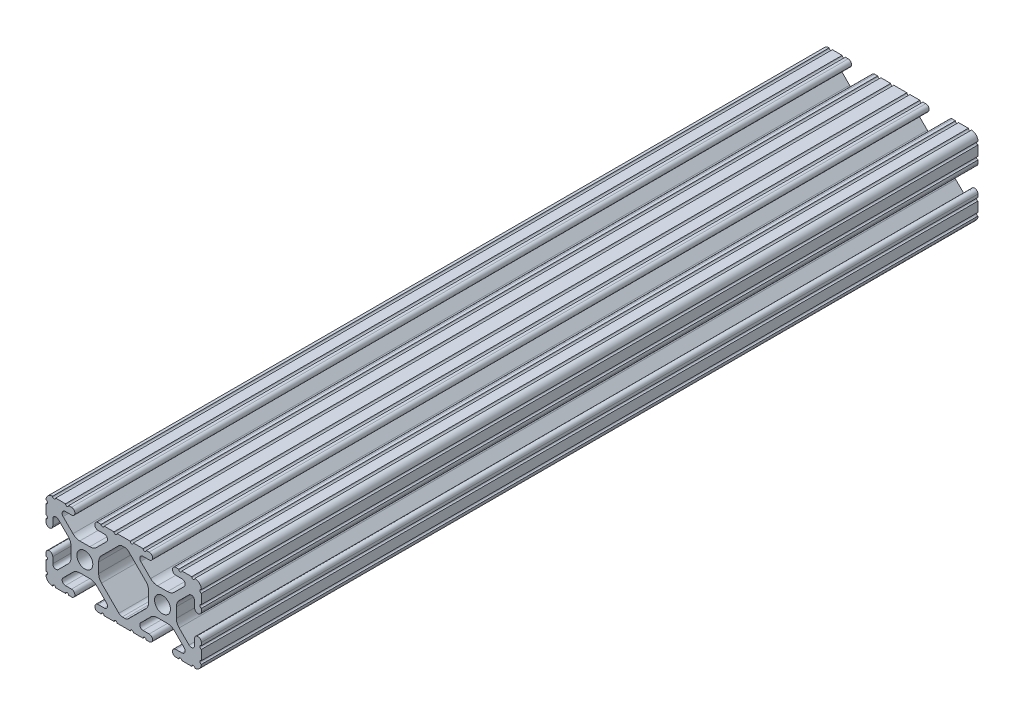
SolidWorks part; units mm, degrees
material "6105-T5 Aluminum"
ref_plane "Front Plane" through (0, 0, 0) normal (0, 0, 1) x (1, 0, 0)
ref_plane "Top Plane" through (0, 0, 0) normal (0, 1, 0) x (1, 0, 0)
ref_plane "Right Plane" through (0, 0, 0) normal (1, 0, 0) x (0, 0, -1)
sketch "Sketch1" plane through (0, 0, 0) normal (0, 0, 1) x (1, 0, 0)
  line L0 (-8.1828, -1.6394) -> (-8.1828, 1.6394)
  line L1 (-7.2529, 3.8844) -> (-1.5656, 9.5718)
  line L2 (-0.452, 10.033) -> (0.452, 10.033)
  line L3 (1.5656, 9.5718) -> (7.2529, 3.8844)
  line L4 (8.1828, 1.6394) -> (8.1828, -1.6394)
  line L5 (7.2529, -3.8844) -> (1.5656, -9.5718)
  line L6 (0.452, -10.033) -> (-0.452, -10.033)
  line L7 (-1.5656, -9.5718) -> (-7.2529, -3.8844)
  line L8 (25.4, -10.5918) -> (25.4, -10.5664)
  line L9 (25.4, -9.5504) -> (25.4, -6.3246)
  line L10 (25.4, -5.3086) -> (25.4, -4.3561)
  line L11 (23.1902, -4.3561) -> (23.1902, -6.3701)
  line L12 (21.3817, -7.1192) -> (18.1471, -3.8846)
  line L13 (17.2172, -1.6396) -> (17.2172, 1.6396)
  line L14 (18.1471, 3.8846) -> (21.3817, 7.1192)
  line L15 (23.1902, 6.3701) -> (23.1902, 4.3561)
  line L16 (25.4, 4.3561) -> (25.4, 5.3086)
  line L17 (25.4, 6.3246) -> (25.4, 9.5504)
  line L18 (25.4, 10.5664) -> (25.4, 10.5918)
  line L19 (23.2918, 12.7) -> (23.2664, 12.7)
  line L20 (22.2504, 12.7) -> (19.0246, 12.7)
  line L21 (18.0086, 12.7) -> (17.0561, 12.7)
  line L22 (17.0561, 10.4902) -> (19.0701, 10.4902)
  line L23 (19.8192, 8.6817) -> (16.5846, 5.4471)
  line L24 (14.3396, 4.5172) -> (11.0604, 4.5172)
  line L25 (8.8154, 5.4471) -> (5.5808, 8.6817)
  line L26 (6.3299, 10.4902) -> (8.3439, 10.4902)
  line L27 (8.3439, 12.7) -> (7.3914, 12.7)
  line L28 (6.3754, 12.7) -> (3.1496, 12.7)
  line L29 (2.1336, 12.7) -> (-2.1336, 12.7)
  line L30 (-3.1496, 12.7) -> (-6.3754, 12.7)
  line L31 (-7.3914, 12.7) -> (-8.3439, 12.7)
  line L32 (-8.3439, 10.4902) -> (-6.3299, 10.4902)
  line L33 (-5.5808, 8.6817) -> (-8.8154, 5.4471)
  line L34 (-11.0604, 4.5172) -> (-14.3396, 4.5172)
  line L35 (-16.5846, 5.4471) -> (-19.8192, 8.6817)
  line L36 (-19.0701, 10.4902) -> (-17.0561, 10.4902)
  line L37 (-17.0561, 12.7) -> (-18.0086, 12.7)
  line L38 (-19.0246, 12.7) -> (-22.2504, 12.7)
  line L39 (-23.2664, 12.7) -> (-23.2918, 12.7)
  line L40 (-25.4, 10.5918) -> (-25.4, 10.5664)
  line L41 (-25.4, 9.5504) -> (-25.4, 6.3246)
  line L42 (-25.4, 5.3086) -> (-25.4, 4.3561)
  line L43 (-23.1902, 4.3561) -> (-23.1902, 6.3701)
  line L44 (-21.3817, 7.1192) -> (-18.1471, 3.8846)
  line L45 (-17.2172, 1.6396) -> (-17.2172, -1.6396)
  line L46 (-18.1471, -3.8846) -> (-21.3817, -7.1192)
  line L47 (-23.1902, -6.3701) -> (-23.1902, -4.3561)
  line L48 (-25.4, -4.3561) -> (-25.4, -5.3086)
  line L49 (-25.4, -6.3246) -> (-25.4, -9.5504)
  line L50 (-25.4, -10.5664) -> (-25.4, -10.5918)
  line L51 (-23.2918, -12.7) -> (-23.2664, -12.7)
  line L52 (-22.2504, -12.7) -> (-19.0246, -12.7)
  line L53 (-18.0086, -12.7) -> (-17.0561, -12.7)
  line L54 (-17.0561, -10.4902) -> (-19.0701, -10.4902)
  line L55 (-19.8192, -8.6817) -> (-16.5846, -5.4471)
  line L56 (-14.3396, -4.5172) -> (-11.0604, -4.5172)
  line L57 (-8.8154, -5.4471) -> (-5.5808, -8.6817)
  line L58 (-6.3299, -10.4902) -> (-8.3439, -10.4902)
  line L59 (-8.3439, -12.7) -> (-7.3914, -12.7)
  line L60 (-6.3754, -12.7) -> (-3.1496, -12.7)
  line L61 (-2.1336, -12.7) -> (2.1336, -12.7)
  line L62 (3.1496, -12.7) -> (6.3754, -12.7)
  line L63 (7.3914, -12.7) -> (8.3439, -12.7)
  line L64 (8.3439, -10.4902) -> (6.3299, -10.4902)
  line L65 (5.5808, -8.6817) -> (8.8154, -5.4471)
  line L66 (11.0604, -4.5172) -> (14.3396, -4.5172)
  line L67 (16.5846, -5.4471) -> (19.8192, -8.6817)
  line L68 (19.0701, -10.4902) -> (17.0561, -10.4902)
  line L69 (17.0561, -12.7) -> (18.0086, -12.7)
  line L70 (19.0246, -12.7) -> (22.2504, -12.7)
  line L71 (23.2664, -12.7) -> (23.2918, -12.7)
  circle A0 centre (-12.7, 0) radius 2.6035
  circle A1 centre (12.7, 0) radius 2.6035
  arc A2 (-8.1828, -1.6394) -> (-7.2529, -3.8844) centre (-5.0078, -1.6394) ccw
  arc A3 (-7.2529, 3.8844) -> (-8.1828, 1.6394) centre (-5.0078, 1.6394) ccw
  arc A4 (-0.452, 10.033) -> (-1.5656, 9.5718) centre (-0.452, 8.4582) ccw
  arc A5 (1.5656, 9.5718) -> (0.452, 10.033) centre (0.452, 8.4582) ccw
  arc A6 (8.1828, 1.6394) -> (7.2529, 3.8844) centre (5.0078, 1.6394) ccw
  arc A7 (7.2529, -3.8844) -> (8.1828, -1.6394) centre (5.0078, -1.6394) ccw
  arc A8 (0.452, -10.033) -> (1.5656, -9.5718) centre (0.452, -8.4582) ccw
  arc A9 (-1.5656, -9.5718) -> (-0.452, -10.033) centre (-0.452, -8.4582) ccw
  arc A10 (23.2918, -12.7) -> (25.4, -10.5918) centre (23.2918, -10.5918) ccw
  arc A11 (25.4, -9.5504) -> (25.4, -10.5664) centre (25.4, -10.0584) ccw
  arc A12 (25.4, -5.3086) -> (25.4, -6.3246) centre (25.4, -5.8166) ccw
  arc A13 (25.4, -4.3561) -> (23.1902, -4.3561) centre (24.2951, -4.3561) ccw
  arc A14 (21.3817, -7.1192) -> (23.1902, -6.3701) centre (22.1308, -6.3701) ccw
  arc A15 (17.2172, -1.6396) -> (18.1471, -3.8846) centre (20.3922, -1.6396) ccw
  arc A16 (18.1471, 3.8846) -> (17.2172, 1.6396) centre (20.3922, 1.6396) ccw
  arc A17 (23.1902, 6.3701) -> (21.3817, 7.1192) centre (22.1308, 6.3701) ccw
  arc A18 (23.1902, 4.3561) -> (25.4, 4.3561) centre (24.2951, 4.3561) ccw
  arc A19 (25.4, 6.3246) -> (25.4, 5.3086) centre (25.4, 5.8166) ccw
  arc A20 (25.4, 10.5664) -> (25.4, 9.5504) centre (25.4, 10.0584) ccw
  arc A21 (25.4, 10.5918) -> (23.2918, 12.7) centre (23.2918, 10.5918) ccw
  arc A22 (22.2504, 12.7) -> (23.2664, 12.7) centre (22.7584, 12.7) ccw
  arc A23 (18.0086, 12.7) -> (19.0246, 12.7) centre (18.5166, 12.7) ccw
  arc A24 (17.0561, 12.7) -> (17.0561, 10.4902) centre (17.0561, 11.5951) ccw
  arc A25 (19.8192, 8.6817) -> (19.0701, 10.4902) centre (19.0701, 9.4308) ccw
  arc A26 (14.3396, 4.5172) -> (16.5846, 5.4471) centre (14.3396, 7.6922) ccw
  arc A27 (8.8154, 5.4471) -> (11.0604, 4.5172) centre (11.0604, 7.6922) ccw
  arc A28 (6.3299, 10.4902) -> (5.5808, 8.6817) centre (6.3299, 9.4308) ccw
  arc A29 (8.3439, 10.4902) -> (8.3439, 12.7) centre (8.3439, 11.5951) ccw
  arc A30 (6.3754, 12.7) -> (7.3914, 12.7) centre (6.8834, 12.7) ccw
  arc A31 (2.1336, 12.7) -> (3.1496, 12.7) centre (2.6416, 12.7) ccw
  arc A32 (-3.1496, 12.7) -> (-2.1336, 12.7) centre (-2.6416, 12.7) ccw
  arc A33 (-7.3914, 12.7) -> (-6.3754, 12.7) centre (-6.8834, 12.7) ccw
  arc A34 (-8.3439, 12.7) -> (-8.3439, 10.4902) centre (-8.3439, 11.5951) ccw
  arc A35 (-5.5808, 8.6817) -> (-6.3299, 10.4902) centre (-6.3299, 9.4308) ccw
  arc A36 (-11.0604, 4.5172) -> (-8.8154, 5.4471) centre (-11.0604, 7.6922) ccw
  arc A37 (-16.5846, 5.4471) -> (-14.3396, 4.5172) centre (-14.3396, 7.6922) ccw
  arc A38 (-19.0701, 10.4902) -> (-19.8192, 8.6817) centre (-19.0701, 9.4308) ccw
  arc A39 (-17.0561, 10.4902) -> (-17.0561, 12.7) centre (-17.0561, 11.5951) ccw
  arc A40 (-19.0246, 12.7) -> (-18.0086, 12.7) centre (-18.5166, 12.7) ccw
  arc A41 (-23.2664, 12.7) -> (-22.2504, 12.7) centre (-22.7584, 12.7) ccw
  arc A42 (-23.2918, 12.7) -> (-25.4, 10.5918) centre (-23.2918, 10.5918) ccw
  arc A43 (-25.4, 9.5504) -> (-25.4, 10.5664) centre (-25.4, 10.0584) ccw
  arc A44 (-25.4, 5.3086) -> (-25.4, 6.3246) centre (-25.4, 5.8166) ccw
  arc A45 (-25.4, 4.3561) -> (-23.1902, 4.3561) centre (-24.2951, 4.3561) ccw
  arc A46 (-21.3817, 7.1192) -> (-23.1902, 6.3701) centre (-22.1308, 6.3701) ccw
  arc A47 (-17.2172, 1.6396) -> (-18.1471, 3.8846) centre (-20.3922, 1.6396) ccw
  arc A48 (-18.1471, -3.8846) -> (-17.2172, -1.6396) centre (-20.3922, -1.6396) ccw
  arc A49 (-23.1902, -6.3701) -> (-21.3817, -7.1192) centre (-22.1308, -6.3701) ccw
  arc A50 (-23.1902, -4.3561) -> (-25.4, -4.3561) centre (-24.2951, -4.3561) ccw
  arc A51 (-25.4, -6.3246) -> (-25.4, -5.3086) centre (-25.4, -5.8166) ccw
  arc A52 (-25.4, -10.5664) -> (-25.4, -9.5504) centre (-25.4, -10.0584) ccw
  arc A53 (-25.4, -10.5918) -> (-23.2918, -12.7) centre (-23.2918, -10.5918) ccw
  arc A54 (-22.2504, -12.7) -> (-23.2664, -12.7) centre (-22.7584, -12.7) ccw
  arc A55 (-18.0086, -12.7) -> (-19.0246, -12.7) centre (-18.5166, -12.7) ccw
  arc A56 (-17.0561, -12.7) -> (-17.0561, -10.4902) centre (-17.0561, -11.5951) ccw
  arc A57 (-19.8192, -8.6817) -> (-19.0701, -10.4902) centre (-19.0701, -9.4308) ccw
  arc A58 (-14.3396, -4.5172) -> (-16.5846, -5.4471) centre (-14.3396, -7.6922) ccw
  arc A59 (-8.8154, -5.4471) -> (-11.0604, -4.5172) centre (-11.0604, -7.6922) ccw
  arc A60 (-6.3299, -10.4902) -> (-5.5808, -8.6817) centre (-6.3299, -9.4308) ccw
  arc A61 (-8.3439, -10.4902) -> (-8.3439, -12.7) centre (-8.3439, -11.5951) ccw
  arc A62 (-6.3754, -12.7) -> (-7.3914, -12.7) centre (-6.8834, -12.7) ccw
  arc A63 (-2.1336, -12.7) -> (-3.1496, -12.7) centre (-2.6416, -12.7) ccw
  arc A64 (3.1496, -12.7) -> (2.1336, -12.7) centre (2.6416, -12.7) ccw
  arc A65 (7.3914, -12.7) -> (6.3754, -12.7) centre (6.8834, -12.7) ccw
  arc A66 (8.3439, -12.7) -> (8.3439, -10.4902) centre (8.3439, -11.5951) ccw
  arc A67 (5.5808, -8.6817) -> (6.3299, -10.4902) centre (6.3299, -9.4308) ccw
  arc A68 (11.0604, -4.5172) -> (8.8154, -5.4471) centre (11.0604, -7.6922) ccw
  arc A69 (16.5846, -5.4471) -> (14.3396, -4.5172) centre (14.3396, -7.6922) ccw
  arc A70 (19.0701, -10.4902) -> (19.8192, -8.6817) centre (19.0701, -9.4308) ccw
  arc A71 (17.0561, -10.4902) -> (17.0561, -12.7) centre (17.0561, -11.5951) ccw
  arc A72 (19.0246, -12.7) -> (18.0086, -12.7) centre (18.5166, -12.7) ccw
  arc A73 (23.2664, -12.7) -> (22.2504, -12.7) centre (22.7584, -12.7) ccw
extrude "Extrude1" add sketch "Sketch1" against normal blind 254
